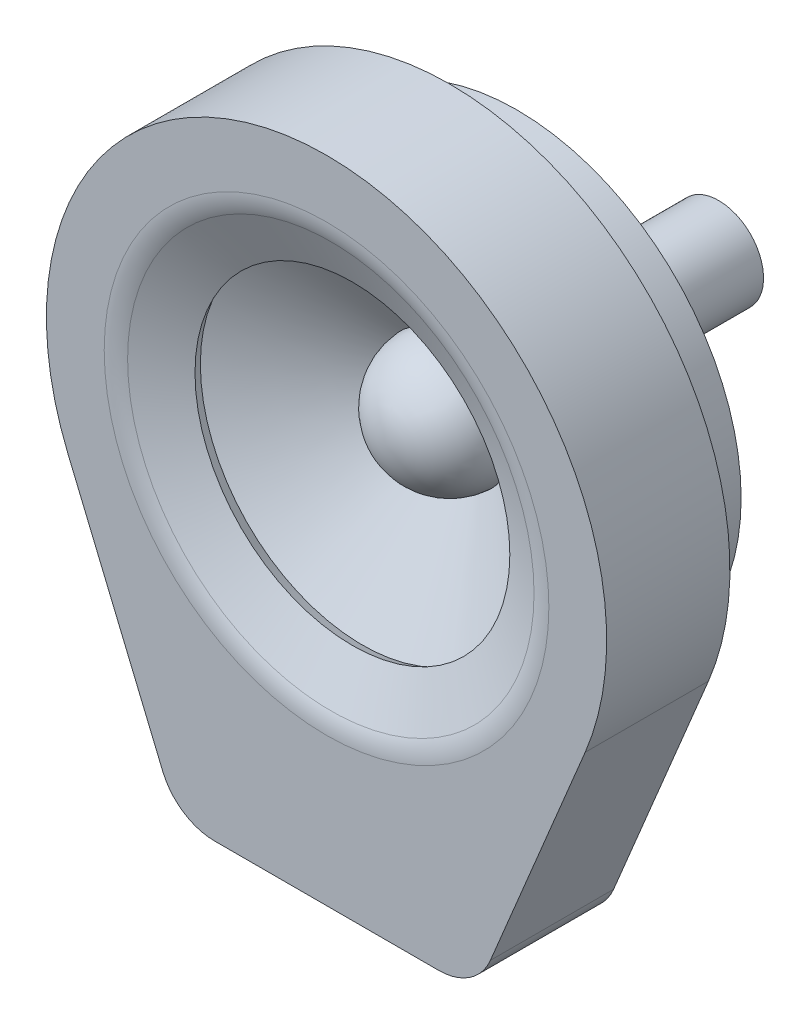
SolidWorks part; units mm, degrees
ref_plane "Front" through (0, 0, 0) normal (0, 0, 1) x (1, 0, 0)
ref_plane "Top" through (0, 0, 0) normal (0, 1, 0) x (1, 0, 0)
ref_plane "Right" through (0, 0, 0) normal (1, 0, 0) x (0, 0, -1)
other "Configuration Table"
sketch "Sketch1" plane through (0, 0, 0) normal (1, 0, 0) x (0, 0, -1)
  line L0 (0, 0) -> (-5.9446, 0) construction
  line L1 (0, 0) -> (12, 0)
  line L3 (12, 0) -> (12, 2)
  line L4 (12, 2) -> (3, 2)
  line L5 (3, 2) -> (3, 10)
  line L6 (3, 10) -> (0, 10)
  line L7 (0, 10) -> (0, 0)
  dimension "D1" = 4
  dimension "D2" = 10
  dimension "D3" = 3
  dimension "D4" = 12
revolve "Revolve1" add sketch "Sketch1" angle 360 about L0
sketch "Sketch2" plane through (0, 0, 0) normal (1, 0, 0) x (0, 0, -1)
  line L0 (0, 0) -> (-2.779, 0) construction
  line L1 (0, 0) -> (-5.9446, 0) construction
  line L2 (0, 2.779) -> (-3.5917, 9)
  line L3 (0, 10) -> (0, -10) construction
  line L4 (-3.5917, 9) -> (-3.5917, 11)
  line L5 (3, 10) -> (0, 10) construction
  arc A0 (-2.779, 0) -> (0, 2.779) centre (0, 0) cw
  dimension "D1" = 30
  dimension "D2" = 1
  dimension "D3" = 2
revolve "Revolve-Thin2" add sketch "Sketch2" angle 360 about L0 wall 0.1
sketch "Sketch4" plane through (0, 0, 0) normal (0, 0, 1) x (1, 0, 0)
  line L0 (0, 0) -> (0, -16) construction
  line L1 (-5.0019, -16) -> (5.0019, -16)
  line L2 (6.8481, -14.7689) -> (11.0776, -4.6137)
  line L3 (-6.8481, -14.7689) -> (-11.0776, -4.6137)
  arc A1 (-6.8481, -14.7689) -> (-5.0019, -16) centre (-5.0019, -14) ccw
  circle A2 centre (0, 0) radius 12
  arc A3 (11.0776, -4.6137) -> (-11.0776, -4.6137) centre (0, 0) ccw
  arc A4 (5.0019, -16) -> (6.8481, -14.7689) centre (5.0019, -14) ccw
  point P9 (-6.3354, -16)
  point P12 (6.3354, -16)
  dimension "D2" = 16
  dimension "D4" = 2
  dimension "D1" = 1
extrude "Extrude-Thin1" add sketch "Sketch4" along normal blind 5 thin
sketch "Sketch5" plane through (0, 0, 5) normal (0, 0, 1) x (1, 0, 0)
  line L3 (-11.5392, -4.8059) -> (-7.3097, -14.9612)
  line L4 (-5.0019, -16.5) -> (5.0019, -16.5)
  line L5 (7.3097, -14.9612) -> (11.5392, -4.8059)
  line L6 (-11.5392, -4.8059) -> (-7.3097, -14.9612)
  line L7 (-5.0019, -16.5) -> (5.0019, -16.5)
  line L8 (7.3097, -14.9612) -> (11.5392, -4.8059)
  arc A3 (11.5392, -4.8059) -> (-11.5392, -4.8059) centre (0, 0) ccw
  arc A4 (-7.3097, -14.9612) -> (-5.0019, -16.5) centre (-5.0019, -14) ccw
  arc A5 (5.0019, -16.5) -> (7.3097, -14.9612) centre (5.0019, -14) ccw
  arc A6 (11.5392, -4.8059) -> (-11.5392, -4.8059) centre (0, 0) ccw
  arc A7 (-7.3097, -14.9612) -> (-5.0019, -16.5) centre (-5.0019, -14) ccw
  arc A8 (5.0019, -16.5) -> (7.3097, -14.9612) centre (5.0019, -14) ccw
  circle A9 centre (0, 0) radius 9.9732
  circle A10 centre (0, 0) radius 9.9732
  dimension "D1" = 0
  dimension "D2" = 1
extrude "Extrude1" add sketch "Sketch5" along normal blind 0.5
sketch "Sketch6" plane through (0, 0, 0) normal (1, 0, 0) x (0, 0, -1)
  line L0 (-5.5, 9.9732) -> (-5.5, 9.4732)
  line L1 (-5.5, 12.5) -> (-5.5, -4.8059) construction
  line L2 (-5.5, 9.4732) -> (-4.3454, 7.0247)
  line L3 (0, 0) -> (-2.0776, 0) construction
  line L4 (0, 0) -> (-5.9446, 0) construction
  dimension "D1" = 0.5
revolve "Revolve-Thin3" add sketch "Sketch6" angle 360 about L3 wall 0.5
fillet "Fillet1" radius 2 1 edges at (-9.4732, 0, 5.5)
